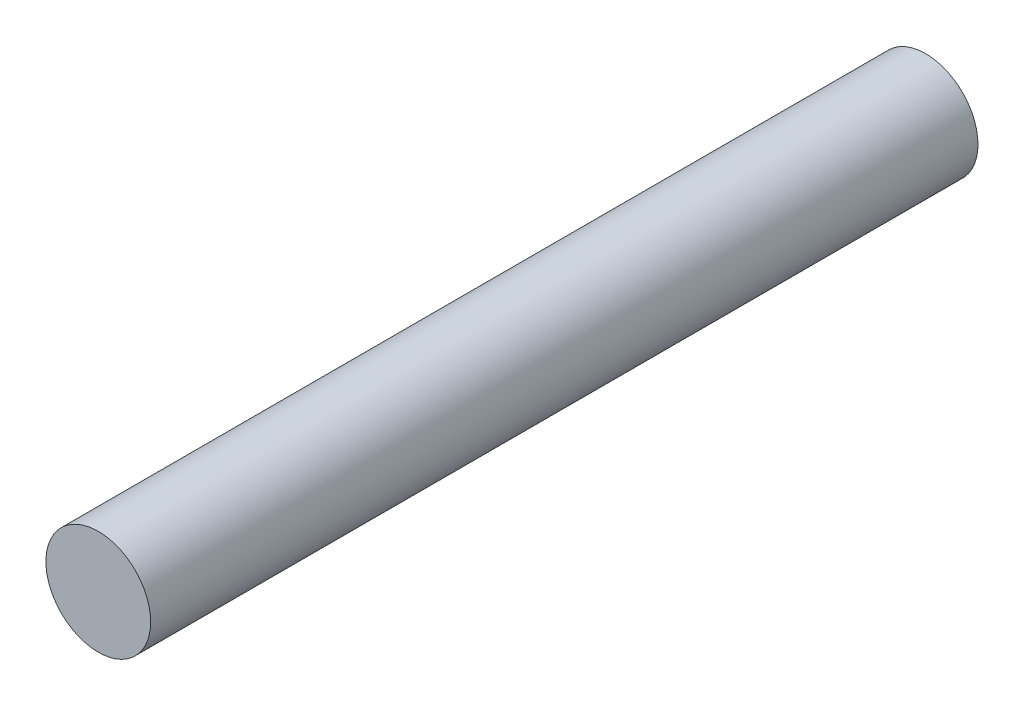
SolidWorks part; units mm, degrees
material "1060 Alloy"
ref_plane "Front Plane" through (0, 0, 0) normal (0, 0, 1) x (1, 0, 0)
ref_plane "Top Plane" through (0, 0, 0) normal (0, 1, 0) x (1, 0, 0)
ref_plane "Right Plane" through (0, 0, 0) normal (1, 0, 0) x (0, 0, -1)
sketch "Sketch1" plane through (0, 0, 0) normal (0, 0, 1) x (1, 0, 0)
  circle A0 centre (0, 0) radius 1
  dimension "D1" = 2
extrude "Boss-Extrude1" add sketch "Sketch1" along normal mid plane 15.8
